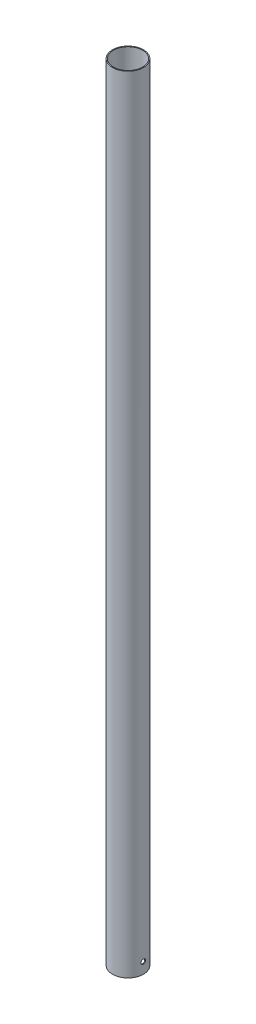
SolidWorks part; units mm, degrees
material "AISI 1035 Steel (SS)"
ref_plane "Front Plane" through (0, 0, 0) normal (0, 0, 1) x (1, 0, 0)
ref_plane "Top Plane" through (0, 0, 0) normal (0, 1, 0) x (1, 0, 0)
ref_plane "Right Plane" through (0, 0, 0) normal (1, 0, 0) x (0, 0, -1)
sketch "Sketch1" plane through (0, 0, 0) normal (0, 1, 0) x (1, 0, 0)
  circle A0 centre (0, 0) radius 70.65
  circle A1 centre (0, 0) radius 66.69
  dimension "D1" = 141.3
  dimension "D2" = 3.96
extrude "Boss-Extrude1" add sketch "Sketch1" along normal blind 3588
sketch "Sketch3" plane through (0, 0, 0) normal (1, 0, 0) x (0, 0, -1)
  circle A0 centre (0, 50) radius 10.5
  dimension "D1" = 21
  dimension "D2" = 50
extrude "Cut-Extrude1" cut sketch "Sketch3" along normal up to next
